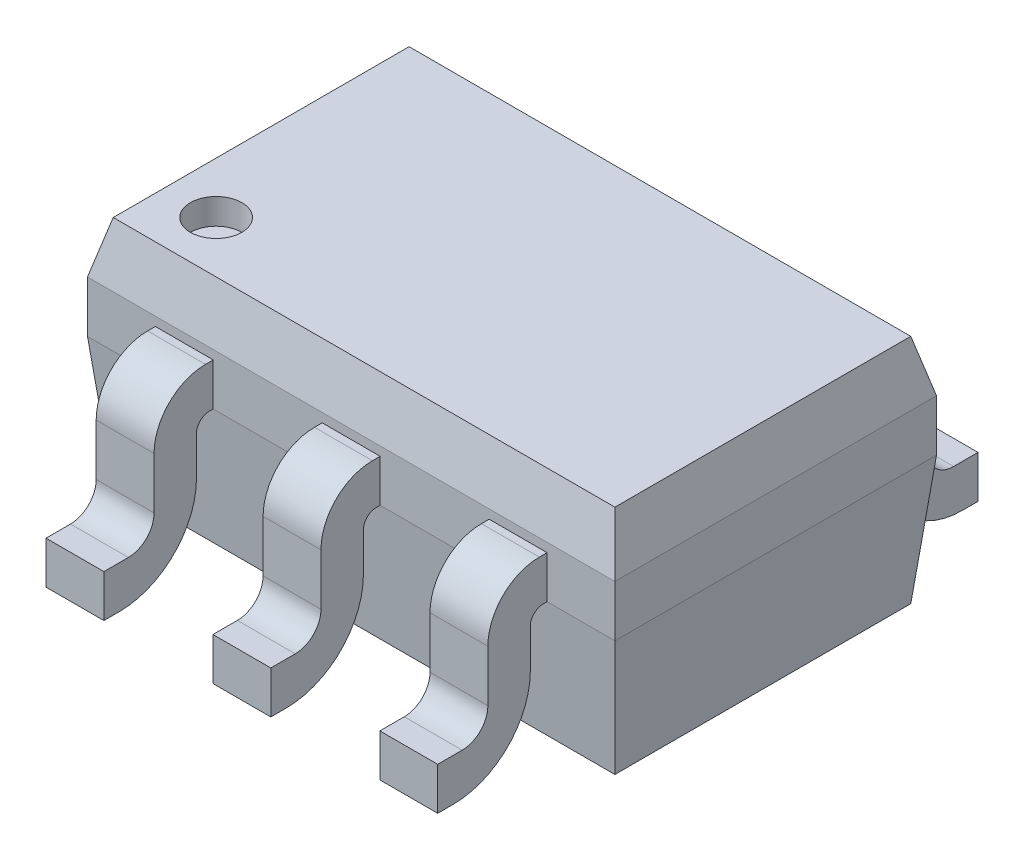
SolidWorks part; units mm, degrees
ref_plane "Front Plane" through (0, 0, 0) normal (0, 0, 1) x (1, 0, 0)
ref_plane "Top Plane" through (0, 0, 0) normal (0, 1, 0) x (1, 0, 0)
ref_plane "Right Plane" through (0, 0, 0) normal (1, 0, 0) x (0, 0, -1)
sketch "Sketch1" plane through (0, 0, 0) normal (0, 1, 0) x (1, 0, 0)
  line L1 (-1.025, -0.625) -> (1.025, -0.625)
  line L2 (-1.025, -0.625) -> (-1.025, 0.625)
  line L3 (-1.025, 0.625) -> (1.025, 0.625)
  line L4 (1.025, -0.625) -> (1.025, 0.625)
  line L5 (-1.025, -0.625) -> (1.025, 0.625) construction
  line L6 (-1.025, 0.625) -> (1.025, -0.625) construction
  point P0 (0, 0)
  dimension "D1" = 1.25
  dimension "D2" = 2.05
extrude "Boss-Extrude1" add sketch "Sketch1" along normal blind 0.9
sketch "Sketch2" plane through (1.025, 0, 0) normal (1, 0, 0) x (0, 0, -1)
  line L0 (-0.625, 0) -> (-1.05, 0) construction
  line L21 (0, 0.9) -> (0, 0) construction
  line L22 (-0.625, 0.9) -> (0.625, 0.9) construction
  line L23 (-0.625, 0.665) -> (-0.655, 0.665)
  line L24 (-0.855, 0.465) -> (-0.855, 0.265)
  line L25 (-0.955, 0.165) -> (-1.05, 0.165)
  line L26 (-1.05, 0.165) -> (-1.05, 0)
  line L27 (-1.05, 0) -> (-0.99, 0)
  line L28 (-0.69, 0.3) -> (-0.69, 0.45)
  line L29 (-0.64, 0.5) -> (-0.625, 0.5)
  line L30 (-0.625, 0.9) -> (-0.625, 0) construction
  line L32 (-0.625, 0.5) -> (-0.625, 0.665)
  line L33 (1.05, 0.165) -> (1.05, 0)
  line L34 (1.05, 0) -> (0.99, 0)
  line L35 (0.64, 0.5) -> (0.625, 0.5)
  line L36 (0.69, 0.3) -> (0.69, 0.45)
  line L37 (0.955, 0.165) -> (1.05, 0.165)
  line L38 (0.855, 0.465) -> (0.855, 0.265)
  line L39 (0.625, 0.665) -> (0.655, 0.665)
  line L40 (0.625, 0.665) -> (0.625, 0.5)
  arc A0 (-0.99, 0) -> (-0.69, 0.3) centre (-0.99, 0.3) ccw
  arc A1 (-0.855, 0.465) -> (-0.655, 0.665) centre (-0.655, 0.465) cw
  arc A2 (-0.855, 0.265) -> (-0.955, 0.165) centre (-0.955, 0.265) cw
  arc A3 (-0.69, 0.45) -> (-0.64, 0.5) centre (-0.64, 0.45) cw
  arc A4 (0.99, 0) -> (0.69, 0.3) centre (0.99, 0.3) cw
  arc A5 (0.69, 0.45) -> (0.64, 0.5) centre (0.64, 0.45) ccw
  arc A6 (0.855, 0.265) -> (0.955, 0.165) centre (0.955, 0.265) ccw
  arc A7 (0.855, 0.465) -> (0.655, 0.665) centre (0.655, 0.465) ccw
  point P8 (-0.6325, 0.5)
  point P20 (-0.69, 0)
  point P23 (-0.855, 0.665)
  point P26 (-0.855, 0.165)
  point P45 (0.855, 0.165)
  point P46 (0.855, 0.665)
  dimension "D8" = 0.3
  dimension "D9" = 0.2
  dimension "D10" = 0.1
  dimension "D11" = 0.05
  dimension "D1" = 0.425
  dimension "D2" = 0.36
  dimension "D3" = 0.165
  dimension "D4" = 0.165
  dimension "D5" = 0.5
  dimension "D6" = 0.165
  dimension "D7" = 0.165
extrude "Boss-Extrude2" add sketch "Sketch2" against normal mid plane 1.5225 from offset 1.025 separate body offset against normal yes
sketch "Sketch3" plane through (0, 0.9, 0) normal (0, 1, 0) x (1, 0, 0)
  line L0 (1.025, 0.625) -> (-1.025, 0.625) construction
  line L1 (-0.5363, 0.625) -> (-0.1125, 0.625)
  line L2 (-0.5363, 0.625) -> (-0.5363, 1.05)
  line L3 (-0.5363, 1.05) -> (-0.1125, 1.05)
  line L4 (-0.1125, 0.625) -> (-0.1125, 1.05)
  line L5 (-0.7612, 1.05) -> (0.7612, 1.05) construction
  line L6 (-1.025, 0) -> (1.025, 0) construction
  line L7 (-1.025, 0.625) -> (-1.025, -0.625) construction
  line L8 (1.025, -0.625) -> (1.025, 0.625) construction
  line L9 (-0.7612, 1.05) -> (-0.7612, 0.955) construction
  line L15 (0, 0) -> (0, 1.05) construction
  line L16 (0, 1.05) -> (-0.1125, 1.05) construction
  line L17 (0.5363, 1.05) -> (0.1125, 1.05)
  line L18 (0.1125, 0.625) -> (0.1125, 1.05)
  line L19 (0.5363, 0.625) -> (0.1125, 0.625)
  line L20 (0.5363, 0.625) -> (0.5363, 1.05)
  line L21 (0.5363, -0.625) -> (0.5363, -1.05)
  line L22 (0.5363, -0.625) -> (0.1125, -0.625)
  line L23 (0.1125, -0.625) -> (0.1125, -1.05)
  line L24 (0.5363, -1.05) -> (0.1125, -1.05)
  line L25 (-0.5363, -1.05) -> (-0.1125, -1.05)
  line L26 (-0.1125, -0.625) -> (-0.1125, -1.05)
  line L27 (-0.5363, -0.625) -> (-0.1125, -0.625)
  line L28 (-0.5363, -0.625) -> (-0.5363, -1.05)
  point P25 (-0.0976, 1.05)
  dimension "D1" = 0.225
  dimension "D3" = 0.1125
extrude "Cut-Extrude2" cut sketch "Sketch3" against normal up to surface (0.9 mm away) up to face at (0, 0, 0)
chamfer "Chamfer1" distance 0.05 distance2 0.5 4 edges at (0, 0, 0.625) (0, 0, -0.625) (1.025, 0, 0) (-1.025, 0, 0)
chamfer "Chamfer2" distance 0.2 distance2 0.05 4 edges at (0, 0.9, 0.625) (0, 0.9, -0.625) (1.025, 0.9, 0) (-1.025, 0.9, 0)
sketch "Sketch4" plane through (0, 0.9, 0) normal (0, 1, 0) x (1, 0, 0)
  line L1 (-0.975, -0.575) -> (0.975, -0.575) construction
  line L2 (-0.975, 0.575) -> (-0.975, -0.575) construction
  circle A0 centre (-0.775, -0.375) radius 0.1
  dimension "D1" = 0.2
  dimension "D2" = 0.2
  dimension "D3" = 0.2
extrude "Cut-Extrude3" cut sketch "Sketch4" against normal blind 0.1
